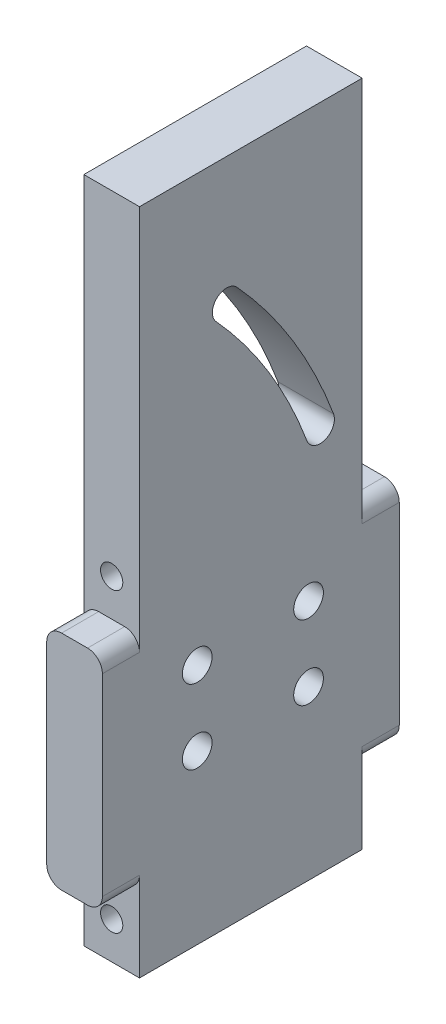
SolidWorks part; units mm, degrees
ref_plane "Front Plane" through (0, 0, 0) normal (0, 0, 1) x (1, 0, 0)
ref_plane "Top Plane" through (0, 0, 0) normal (0, 1, 0) x (1, 0, 0)
ref_plane "Right Plane" through (0, 0, 0) normal (1, 0, 0) x (0, 0, -1)
sketch "Sketch1" plane through (0, 0, 0) normal (1, 0, 0) x (0, 0, -1)
  line L0 (0, 0) -> (0, 25.4)
  line L1 (0, 25.4) -> (-12.7, 25.4)
  line L2 (-12.7, 25.4) -> (-12.7, 101.6)
  line L3 (-12.7, 101.6) -> (0, 101.6)
  line L4 (0, 101.6) -> (0, 228.6)
  line L5 (0, 228.6) -> (76.2, 228.6)
  line L6 (76.2, 228.6) -> (76.2, 101.6)
  line L7 (76.2, 101.6) -> (88.9, 101.6)
  line L8 (88.9, 101.6) -> (88.9, 25.4)
  line L9 (88.9, 25.4) -> (76.2, 25.4)
  line L10 (76.2, 25.4) -> (76.2, 0)
  line L11 (76.2, 0) -> (0, 0)
  dimension "D1" = 101.6
  dimension "D2" = 12.7
  dimension "D3" = 12.7
  dimension "D4" = 228.6
  dimension "D5" = 25.4
  dimension "D6" = 127
extrude "Boss-Extrude1" add sketch "Sketch1" along normal blind 19.05
sketch "Sketch2" plane through (0, 0, 0) normal (0, 0, 1) x (1, 0, 0)
  line L0 (19.05, 101.6) -> (0, 101.6) construction
  circle A0 centre (9.525, 114.3) radius 3.81
  dimension "D1" = 12.7
extrude "Cut-Extrude1" cut sketch "Sketch2" against normal through all
sketch "Sketch3" plane through (0, 0, 0) normal (0, 0, 1) x (1, 0, 0)
  circle A0 centre (9.525, 12.7) radius 3.81
extrude "Cut-Extrude2" cut sketch "Sketch3" against normal through all
sketch "Sketch4" plane through (19.05, 0, 0) normal (1, 0, 0) x (0, 0, -1)
  line L0 (-12.7, 101.6) -> (-12.7, 25.4) construction
  line L2 (0, 0) -> (76.2, 0) construction
  circle A0 centre (19.7551, 57.4153) radius 5.08
  circle A1 centre (57.8551, 57.4153) radius 5.08
  circle A2 centre (19.7551, 82.8153) radius 5.08
  circle A3 centre (57.8551, 82.8153) radius 5.08
  arc A4 (29.8025, 184.728) -> (61.8258, 132.328) centre (-88.9, 76.2) cw construction
  arc A5 (66.389, 134.0273) -> (33.3962, 188.0137) centre (-88.9, 76.2) ccw
  arc A6 (57.2625, 130.6287) -> (26.2088, 181.4423) centre (-88.9, 76.2) ccw
  arc A7 (57.2625, 130.6287) -> (66.389, 134.0273) centre (61.8258, 132.328) ccw
  arc A8 (33.3962, 188.0137) -> (26.2088, 181.4423) centre (29.8025, 184.728) ccw
  point P11 (48.3382, 160.0706)
  dimension "D1" = 2
  dimension "D3" = 76.2
  dimension "D4" = 76.2
  dimension "D2" = 2
extrude "Cut-Extrude3" cut sketch "Sketch4" against normal through all
fillet "Fillet1" radius 5.08 8 edges at (19.05, 25.4, -82.55) (19.05, 101.6, -82.55) (0, 101.6, -82.55) (0, 25.4, -82.55) (0, 25.4, 6.35) (19.05, 25.4, 6.35) (0, 101.6, 6.35) (19.05, 101.6, 6.35)
